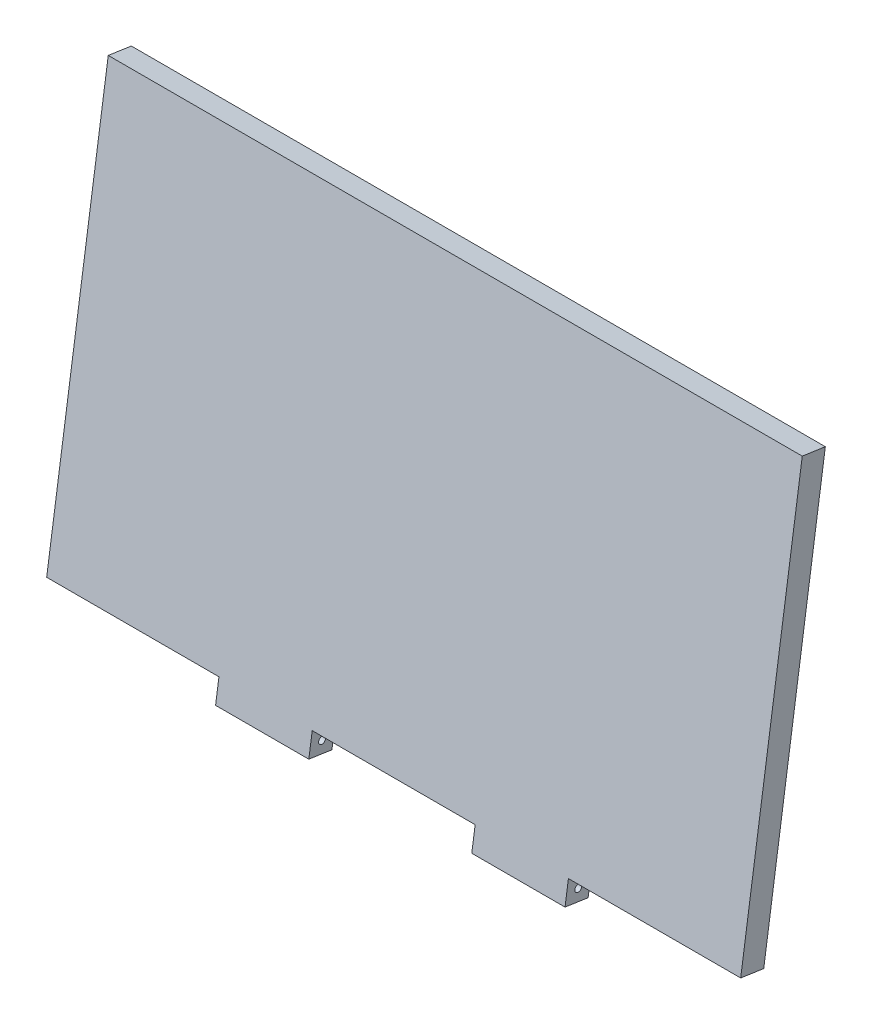
SolidWorks part; units mm, degrees
ref_plane "Front Plane" through (0, 0, 0) normal (0, 0, 1) x (1, 0, 0)
ref_plane "Top Plane" through (0, 0, 0) normal (0, 1, 0) x (1, 0, 0)
ref_plane "Right Plane" through (0, 0, 0) normal (1, 0, 0) x (0, 0, -1)
sketch "Sketch1" plane through (0, 21.9451, 150.1273) normal (0, 0.1446, 0.9895) x (1, 0, 0)
  line L0 (-64.4822, -118.6162) -> (29.3378, -118.6162)
  line L2 (313.4978, -118.6162) -> (313.4978, 113.2057)
  line L3 (313.4978, 113.2057) -> (-64.4822, 113.2057)
  line L4 (-64.4822, -118.6162) -> (-64.4822, 113.2057)
  line L5 (313.4978, -118.6162) -> (-64.4822, 113.2057) construction
  line L6 (313.4978, 113.2057) -> (-64.4822, -118.6162) construction
  line L7 (29.3378, -118.6162) -> (29.3378, -131.3162)
  line L8 (29.3378, -131.3162) -> (80.1378, -131.3162)
  line L9 (80.1378, -131.3162) -> (80.1378, -118.6162)
  line L10 (80.1378, -118.6162) -> (168.8778, -118.6162)
  line L11 (168.8778, -118.6162) -> (168.8778, -131.3162)
  line L12 (168.8778, -131.3162) -> (219.6778, -131.3162)
  line L13 (29.3378, -131.3162) -> (29.3378, -118.6162) construction
  line L14 (219.6778, -131.3162) -> (219.6778, -118.6162)
  line L15 (219.6778, -118.6162) -> (313.4978, -118.6162)
  line L17 (-64.4822, 113.3138) -> (313.4978, 113.3138) construction
  point P0 (124.5078, -2.7053)
  point P6 (0, 0)
  point P11 (293.4789, 64.0775)
  point P12 (-40.2518, 55.914)
  point P13 (274.9826, -142.41)
  point P15 (282.2941, -153.4028)
  point P20 (-59.4022, 73.4472)
  point P21 (301.5153, 49.0185)
  point P22 (0, 0)
  point P25 (-56.8994, -153.4028)
  point P26 (-53.2674, -153.4028)
  point P27 (0, 0)
  point P28 (0, 0)
  point P29 (-57.3521, 171.7712)
  point P30 (-64.4822, -155.1043)
  point P31 (-64.4822, 78.5272)
  point P32 (0, 0)
  point P33 (313.4978, -155.1043)
  point P34 (0, 0)
  point P35 (29.3378, -118.6162)
  point P38 (219.6778, -153.4028)
  point P40 (219.6778, -166.1028)
  point P42 (154.2964, -295.6143)
  point P43 (168.8778, -153.4028)
  point P44 (168.8778, -166.1028)
  point P45 (80.1378, -153.4028)
  point P46 (80.1378, -166.1028)
  point P47 (29.3378, -166.1028)
  point P52 (29.3378, -153.4028)
  point P53 (0, 0)
extrude "Boss-Extrude1" add sketch "Sketch1" along normal blind 12.7
sketch "Sketch3" plane through (29.3378, 0, 0) normal (-1, 0, 0) x (0, 0, 1)
  line L0 (179.8511, -93.5867) -> (181.6881, -106.1531) construction
  line L1 (181.6881, -106.1531) -> (169.1217, -107.9901) construction
  circle A0 centre (174.4864, -100.7884) radius 1.905
  point P0 (0, 0)
  dimension "D3" = 3.81
  dimension "D1" = 6.35
  dimension "D2" = 6.35
extrude "Cut-Extrude1" cut sketch "Sketch3" against normal up to surface (190.34 mm away) up to face at (219.6778, -100.7884, 174.4864)
